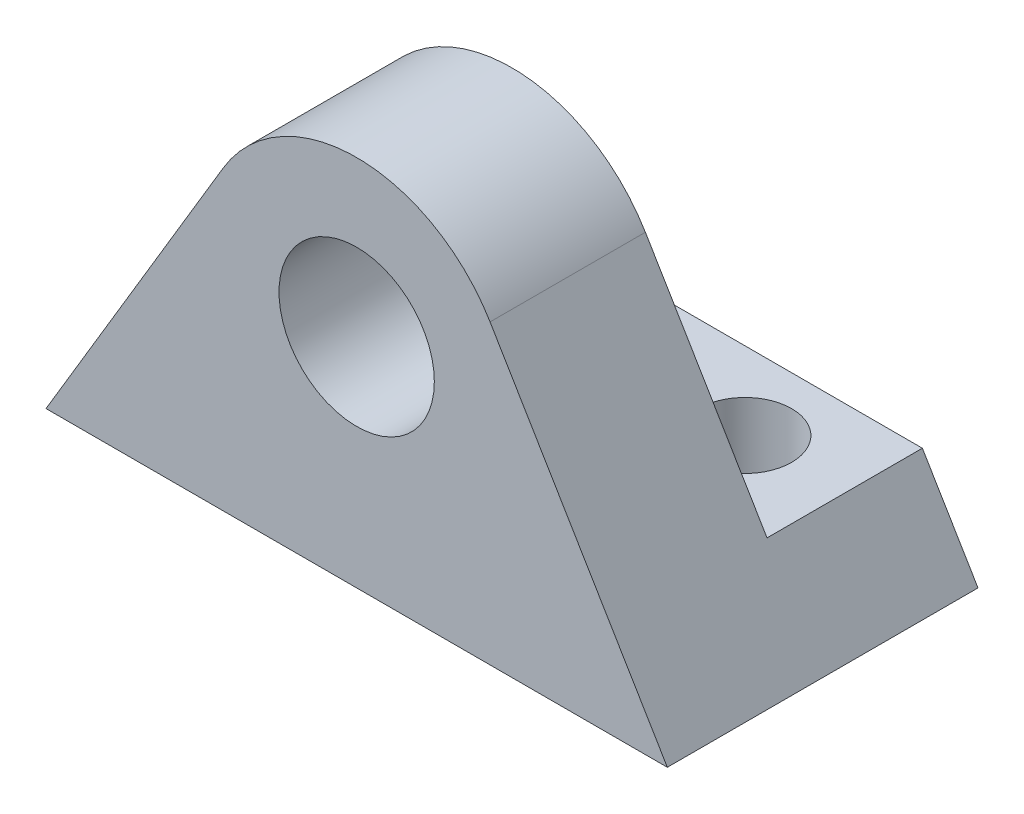
SolidWorks part; units mm, degrees
ref_plane "Front Plane" through (0, 0, 0) normal (0, 0, 1) x (1, 0, 0)
ref_plane "Top Plane" through (0, 0, 0) normal (0, 1, 0) x (1, 0, 0)
ref_plane "Right Plane" through (0, 0, 0) normal (1, 0, 0) x (0, 0, -1)
sketch "Sketch2" plane through (0, 0, 0) normal (0, 0, 1) x (1, 0, 0)
  line L0 (0, 0) -> (25.4, 0)
  line L1 (25.4, 0) -> (18.1528, 12.1441)
  line L2 (7.2472, 12.1441) -> (0, 0)
  circle A0 centre (12.7, 8.89) radius 3.175
  arc A1 (18.1528, 12.1441) -> (7.2472, 12.1441) centre (12.7, 8.89) ccw
  dimension "D2" = 6.35
  dimension "D3" = 6.35
  dimension "D1" = 8.89
  dimension "D4" = 25.4
extrude "Boss-Extrude2" add sketch "Sketch2" along normal mid plane 12.7
sketch "Sketch6" plane through (0, 0, 0) normal (0, 0, 1) x (1, 0, 0)
  line L0 (0, 0) -> (25.4, 0) construction
  line L5 (2.2737, 15.24) -> (23.1263, 15.24)
  line L6 (2.2737, 15.24) -> (2.2737, 3.81)
  line L7 (2.2737, 3.81) -> (23.1263, 3.81)
  line L8 (23.1263, 15.24) -> (23.1263, 3.81)
  line L9 (2.2737, 15.24) -> (23.1263, 3.81) construction
  line L10 (2.2737, 3.81) -> (23.1263, 15.24) construction
  line L11 (7.2472, 12.1441) -> (0, 0) construction
  line L12 (25.4, 0) -> (18.1528, 12.1441) construction
  arc A0 (18.1528, 12.1441) -> (7.2472, 12.1441) centre (12.7, 8.89) ccw construction
  point P0 (12.7, 8.89)
  point P8 (0, 0)
  point P11 (0, 0)
  point P14 (0, 0)
  dimension "D1" = 3.81
extrude "Cut-Extrude3" cut sketch "Sketch6" against normal blind 6.35
sketch "Sketch7" plane through (0, 3.81, 0) normal (0, 1, 0) x (1, 0, 0)
  line L0 (12.7, 6.35) -> (12.7, 0) construction
  line L1 (2.2737, 6.35) -> (23.1263, 6.35) construction
  line L2 (18.1528, 0) -> (7.2472, 0) construction
  line L3 (12.7, 3.175) -> (0, 3.175) construction
  line L4 (0, -6.35) -> (0, 6.35) construction
  circle A0 centre (6.35, 3.175) radius 1.905
  circle A1 centre (19.05, 3.175) radius 1.905
  point P13 (6.35, 3.175)
  dimension "D1" = 3.81
extrude "Cut-Extrude4" cut sketch "Sketch7" against normal blind 6.35
